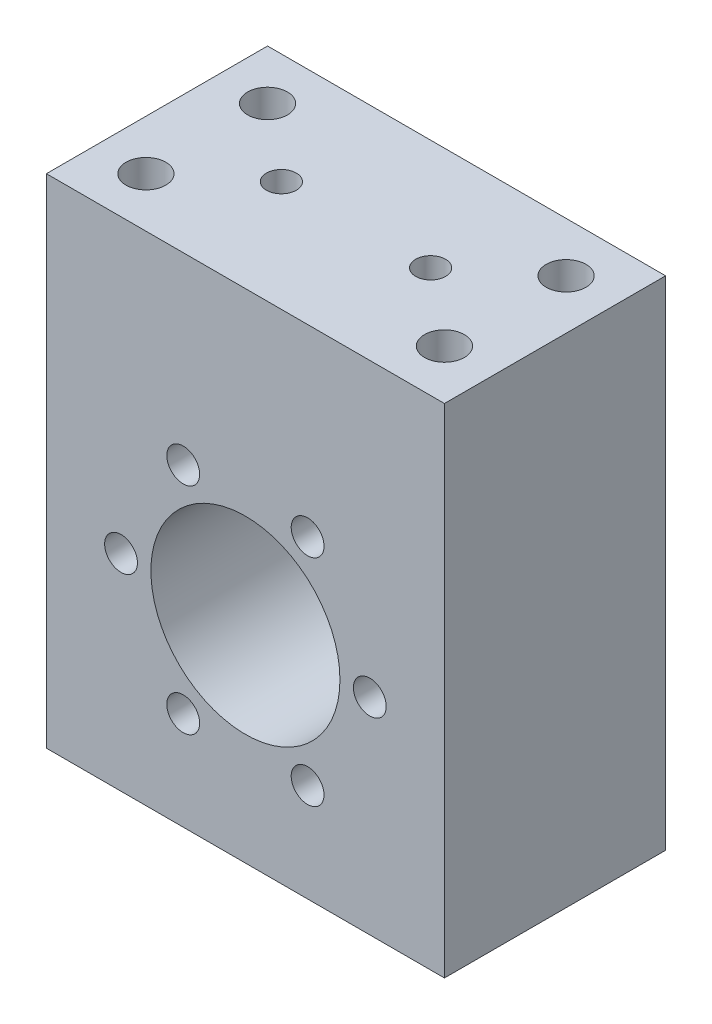
SolidWorks part; units mm, degrees
material "AISI 1020"
ref_plane "Plano frontal" through (0, 0, 0) normal (0, 0, 1) x (1, 0, 0)
ref_plane "Plano superior" through (0, 0, 0) normal (0, 1, 0) x (1, 0, 0)
ref_plane "Plano direito" through (0, 0, 0) normal (1, 0, 0) x (0, 0, -1)
sketch "Esboço2" plane through (0, 0, 0) normal (0, 0, 1) x (1, 0, 0)
  line L1 (-40, -58.6) -> (40, -58.6)
  line L2 (-40, -58.6) -> (-40, 58.6)
  line L3 (-40, 58.6) -> (40, 58.6)
  line L4 (40, -58.6) -> (40, 58.6)
  line L5 (-40, -58.6) -> (40, 58.6) construction
  line L6 (-40, 58.6) -> (40, -58.6) construction
  point P0 (0, 0)
  dimension "D1" = 117.2
  dimension "D2" = 80
extrude "Ressalto-extrusão2" add sketch "Esboço2" along normal mid plane 44.45
sketch "Esboço3" plane through (0, 0, 22.225) normal (0, 0, 1) x (1, 0, 0)
  circle A0 centre (0, 0) radius 19
  dimension "D1" = 38
extrude "Corte-extrusão1" cut sketch "Esboço3" against normal through all
sketch "Esboço4" plane through (0, 0, 22.225) normal (0, 0, 1) x (1, 0, 0)
  circle A0 centre (12.5, 21.6506) radius 3.3
  dimension "D1" = 6.6
  dimension "D2" = 25
  dimension "D3" = 12.5
extrude "Corte-extrusão2" cut sketch "Esboço4" against normal blind 34.5
cosmetic thread "Representação de rosca7" parameters "D2"=8
pattern_circular "PadrãoCircular1" count 6 over 360 about axis through (0, 0, 0) along (0, 0, 1) of "Corte-extrusão2"
cosmetic thread "Representação de rosca5" parameters "D2"=8
cosmetic thread "Representação de rosca6" parameters "D2"=8
cosmetic thread "Representação de rosca8" parameters "D2"=8
cosmetic thread "Representação de rosca9" parameters "D2"=8
cosmetic thread "Representação de rosca10" parameters "D2"=8
sketch "Esboço6" plane through (0, 0, 22.225) normal (0, 0, 1) x (1, 0, 0)
  circle A0 centre (0, 0) radius 31
  dimension "D1" = 62
extrude "Corte-extrusão3" [suppressed] cut sketch "Esboço6" against normal blind 10
sketch "Esboço7" plane through (0, -58.6, 0) normal (0, -1, 0) x (1, 0, 0)
  circle A0 centre (0, 0) radius 7.5
  dimension "D1" = 15
extrude "Corte-extrusão4" [suppressed] cut sketch "Esboço7" against normal blind 20
sketch "Esboço10" plane through (0, 58.6, 0) normal (0, 1, 0) x (1, 0, 0)
  line L1 (-40, -22.225) -> (-40, 22.225) construction
  line L2 (40, 22.225) -> (-40, 22.225) construction
  line L3 (40, -22.225) -> (-40, -22.225) construction
  line L4 (40, -22.225) -> (40, 22.225) construction
  circle A0 centre (-30, 12.225) radius 4
  circle A1 centre (30, 12.225) radius 4
  circle A2 centre (-30, -12.225) radius 4
  circle A3 centre (30, -12.225) radius 4
  circle A4 centre (-15, 0) radius 3
  circle A5 centre (15, 0) radius 3
  point P18 (-40, 0)
  dimension "D1" = 8
  dimension "D2" = 8
  dimension "D5" = 10
  dimension "D6" = 10
  dimension "D3" = 8
  dimension "D7" = 6
  dimension "D8" = 10
  dimension "D9" = 10
  dimension "D10" = 6
  dimension "D11" = 25
  dimension "D12" = 10
  dimension "D13" = 10
  dimension "D14" = 25
  dimension "D15" = 10
  dimension "D16" = 8
  dimension "D4" = 10
extrude "Corte-extrusão5" cut sketch "Esboço10" against normal blind 30
cosmetic thread "Representação de rosca1" parameters "D2"=10
cosmetic thread "Representação de rosca2" parameters "D2"=10
cosmetic thread "Representação de rosca3" parameters "D2"=10
cosmetic thread "Representação de rosca4" parameters "D2"=10
sketch "Esboço11" plane through (0, 0, 22.225) normal (0, 0, 1) x (1, 0, 0)
  line L0 (40, 58.6) -> (-40, 58.6) construction
  line L1 (-10, 58.6) -> (10, 58.6)
  line L2 (-10, 58.6) -> (-10, 51.6)
  line L3 (-10, 51.6) -> (10, 51.6)
  line L4 (10, 58.6) -> (10, 51.6)
  dimension "D1" = 20
  dimension "D2" = 10
  dimension "D3" = 7
extrude "Corte-extrusão6" [suppressed] cut sketch "Esboço11" against normal through all
sketch "Esboço12" plane through (0, 0, 22.225) normal (0, 0, 1) x (1, 0, 0)
  line L0 (40, -58.6) -> (40, 58.6) construction
  line L1 (-40, -58.6) -> (40, -58.6)
  line L2 (-40, -58.6) -> (-40, -41.4)
  line L3 (-40, -41.4) -> (40, -41.4)
  line L4 (40, -58.6) -> (40, -41.4)
  dimension "D1" = 17.2
extrude "Corte-extrusão7" cut sketch "Esboço12" against normal through all
thread "Rosca1" [suppressed] pitch 1.25 start angle 0, offset 0, length 0, pitch 1.25, diameter 8
ref_plane "Plano1" through (-34, 58.6, -12.225) normal (0, 0, 1) x (-1, 0, 0)
sketch "Perfil da rosca1" plane through (-34, 58.6, -12.225) normal (0, 0, 1) x (-1, 0, 0)
  line L0 (0, 0) -> (0, 1.25) construction
  line L11 (0, 0) -> (0, 1.0937)
  line L12 (0, 1.0937) -> (-0.6766, 0.7031)
  line L13 (-0.6766, 0.7031) -> (-0.6766, 0.3906)
  line L15 (-0.6766, 0.3906) -> (0, 0)
  line L17 (-0.6766, 0.5469) -> (0, 0.5469) construction
  point P2 (0, 0)
  dimension "Pitch" = 1.25
  dimension "Profile_Angle" = 60
  dimension "Profile_Land" = 0.3125
  dimension "Profile_Height" = 0.6766
thread "Rosca2" [suppressed] pitch 1.25 start angle 0, offset 0, length 0, pitch 1.25, diameter 8
ref_plane "Plano2" through (-34, 58.6, 12.225) normal (0, 0, 1) x (-1, 0, 0)
sketch "Perfil da rosca2" plane through (-34, 58.6, 12.225) normal (0, 0, 1) x (-1, 0, 0)
  line L0 (0, 0) -> (0, 1.25) construction
  line L11 (0, 0) -> (0, 1.0937)
  line L12 (0, 1.0937) -> (-0.6766, 0.7031)
  line L13 (-0.6766, 0.7031) -> (-0.6766, 0.3906)
  line L15 (-0.6766, 0.3906) -> (0, 0)
  line L17 (-0.6766, 0.5469) -> (0, 0.5469) construction
  point P2 (0, 0)
  dimension "Pitch" = 1.25
  dimension "Profile_Angle" = 60
  dimension "Profile_Land" = 0.3125
  dimension "Profile_Height" = 0.6766
thread "Rosca3" [suppressed] pitch 1.25 start angle 0, offset 0, length 0, pitch 1.25, diameter 8
ref_plane "Plano3" through (26, 58.6, -12.225) normal (0, 0, 1) x (-1, 0, 0)
sketch "Perfil da rosca3" plane through (26, 58.6, -12.225) normal (0, 0, 1) x (-1, 0, 0)
  line L0 (0, 0) -> (0, 1.25) construction
  line L11 (0, 0) -> (0, 1.0937)
  line L12 (0, 1.0937) -> (-0.6766, 0.7031)
  line L13 (-0.6766, 0.7031) -> (-0.6766, 0.3906)
  line L15 (-0.6766, 0.3906) -> (0, 0)
  line L17 (-0.6766, 0.5469) -> (0, 0.5469) construction
  point P2 (0, 0)
  dimension "Pitch" = 1.25
  dimension "Profile_Angle" = 60
  dimension "Profile_Land" = 0.3125
  dimension "Profile_Height" = 0.6766
thread "Rosca4" [suppressed] pitch 1.25 start angle 0, offset 0, length 0, pitch 1.25, diameter 8
ref_plane "Plano4" through (26, 58.6, 12.225) normal (0, 0, 1) x (-1, 0, 0)
sketch "Perfil da rosca4" plane through (26, 58.6, 12.225) normal (0, 0, 1) x (-1, 0, 0)
  line L0 (0, 0) -> (0, 1.25) construction
  line L11 (0, 0) -> (0, 1.0937)
  line L12 (0, 1.0937) -> (-0.6766, 0.7031)
  line L13 (-0.6766, 0.7031) -> (-0.6766, 0.3906)
  line L15 (-0.6766, 0.3906) -> (0, 0)
  line L17 (-0.6766, 0.5469) -> (0, 0.5469) construction
  point P2 (0, 0)
  dimension "Pitch" = 1.25
  dimension "Profile_Angle" = 60
  dimension "Profile_Land" = 0.3125
  dimension "Profile_Height" = 0.6766
thread "Rosca5" [suppressed] pitch 1.25 start angle 0, offset 0, length 0, pitch 1.25, diameter 6.6
ref_plane "Plano5" through (-15.8, 21.6506, 22.225) normal (0, -1, 0) x (-1, 0, 0)
sketch "Perfil da rosca5" plane through (-15.8, 21.6506, 22.225) normal (0, -1, 0) x (-1, 0, 0)
  line L0 (0, 0) -> (0, 1.25) construction
  line L11 (0, 0) -> (0, 1.0937)
  line L12 (0, 1.0937) -> (-0.6766, 0.7031)
  line L13 (-0.6766, 0.7031) -> (-0.6766, 0.3906)
  line L15 (-0.6766, 0.3906) -> (0, 0)
  line L17 (-0.6766, 0.5469) -> (0, 0.5469) construction
  point P2 (0, 0)
  dimension "Pitch" = 1.25
  dimension "Profile_Angle" = 60
  dimension "Profile_Land" = 0.3125
  dimension "Profile_Height" = 0.6766
thread "Rosca6" [suppressed] pitch 1.25 start angle 0, offset 0, length 0, pitch 1.25, diameter 6.6
ref_plane "Plano6" through (9.2, 21.6506, 22.225) normal (0, -1, 0) x (-1, 0, 0)
sketch "Perfil da rosca6" plane through (9.2, 21.6506, 22.225) normal (0, -1, 0) x (-1, 0, 0)
  line L0 (0, 0) -> (0, 1.25) construction
  line L11 (0, 0) -> (0, 1.0937)
  line L12 (0, 1.0937) -> (-0.6766, 0.7031)
  line L13 (-0.6766, 0.7031) -> (-0.6766, 0.3906)
  line L15 (-0.6766, 0.3906) -> (0, 0)
  line L17 (-0.6766, 0.5469) -> (0, 0.5469) construction
  point P2 (0, 0)
  dimension "Pitch" = 1.25
  dimension "Profile_Angle" = 60
  dimension "Profile_Land" = 0.3125
  dimension "Profile_Height" = 0.6766
thread "Rosca7" [suppressed] pitch 1.25 start angle 0, offset 0, length 0, pitch 1.25, diameter 6.6
ref_plane "Plano7" through (-28.3, 0, 22.225) normal (0, -1, 0) x (-1, 0, 0)
sketch "Perfil da rosca7" plane through (-28.3, 0, 22.225) normal (0, -1, 0) x (-1, 0, 0)
  line L0 (0, 0) -> (0, 1.25) construction
  line L11 (0, 0) -> (0, 1.0937)
  line L12 (0, 1.0937) -> (-0.6766, 0.7031)
  line L13 (-0.6766, 0.7031) -> (-0.6766, 0.3906)
  line L15 (-0.6766, 0.3906) -> (0, 0)
  line L17 (-0.6766, 0.5469) -> (0, 0.5469) construction
  point P2 (0, 0)
  dimension "Pitch" = 1.25
  dimension "Profile_Angle" = 60
  dimension "Profile_Land" = 0.3125
  dimension "Profile_Height" = 0.6766
thread "Rosca8" [suppressed] pitch 1.25 start angle 0, offset 0, length 0, pitch 1.25, diameter 6.6
ref_plane "Plano8" through (-15.8, -21.6506, 22.225) normal (0, -1, 0) x (-1, 0, 0)
sketch "Perfil da rosca8" plane through (-15.8, -21.6506, 22.225) normal (0, -1, 0) x (-1, 0, 0)
  line L0 (0, 0) -> (0, 1.25) construction
  line L11 (0, 0) -> (0, 1.0937)
  line L12 (0, 1.0937) -> (-0.6766, 0.7031)
  line L13 (-0.6766, 0.7031) -> (-0.6766, 0.3906)
  line L15 (-0.6766, 0.3906) -> (0, 0)
  line L17 (-0.6766, 0.5469) -> (0, 0.5469) construction
  point P2 (0, 0)
  dimension "Pitch" = 1.25
  dimension "Profile_Angle" = 60
  dimension "Profile_Land" = 0.3125
  dimension "Profile_Height" = 0.6766
thread "Rosca9" [suppressed] pitch 1.25 start angle 0, offset 0, length 0, pitch 1.25, diameter 6.6
ref_plane "Plano9" through (9.2, -21.6506, 22.225) normal (0, -1, 0) x (-1, 0, 0)
sketch "Perfil da rosca9" plane through (9.2, -21.6506, 22.225) normal (0, -1, 0) x (-1, 0, 0)
  line L0 (0, 0) -> (0, 1.25) construction
  line L11 (0, 0) -> (0, 1.0937)
  line L12 (0, 1.0937) -> (-0.6766, 0.7031)
  line L13 (-0.6766, 0.7031) -> (-0.6766, 0.3906)
  line L15 (-0.6766, 0.3906) -> (0, 0)
  line L17 (-0.6766, 0.5469) -> (0, 0.5469) construction
  point P2 (0, 0)
  dimension "Pitch" = 1.25
  dimension "Profile_Angle" = 60
  dimension "Profile_Land" = 0.3125
  dimension "Profile_Height" = 0.6766
thread "Rosca10" [suppressed] pitch 1.25 start angle 0, offset 0, length 0, pitch 1.25, diameter 6.6
ref_plane "Plano10" through (21.7, 0, 22.225) normal (0, -1, 0) x (-1, 0, 0)
sketch "Perfil da rosca10" plane through (21.7, 0, 22.225) normal (0, -1, 0) x (-1, 0, 0)
  line L0 (0, 0) -> (0, 1.25) construction
  line L11 (0, 0) -> (0, 1.0937)
  line L12 (0, 1.0937) -> (-0.6766, 0.7031)
  line L13 (-0.6766, 0.7031) -> (-0.6766, 0.3906)
  line L15 (-0.6766, 0.3906) -> (0, 0)
  line L17 (-0.6766, 0.5469) -> (0, 0.5469) construction
  point P2 (0, 0)
  dimension "Pitch" = 1.25
  dimension "Profile_Angle" = 60
  dimension "Profile_Land" = 0.3125
  dimension "Profile_Height" = 0.6766
chamfer "Chanfro1" [suppressed] distance 20 angle 45
